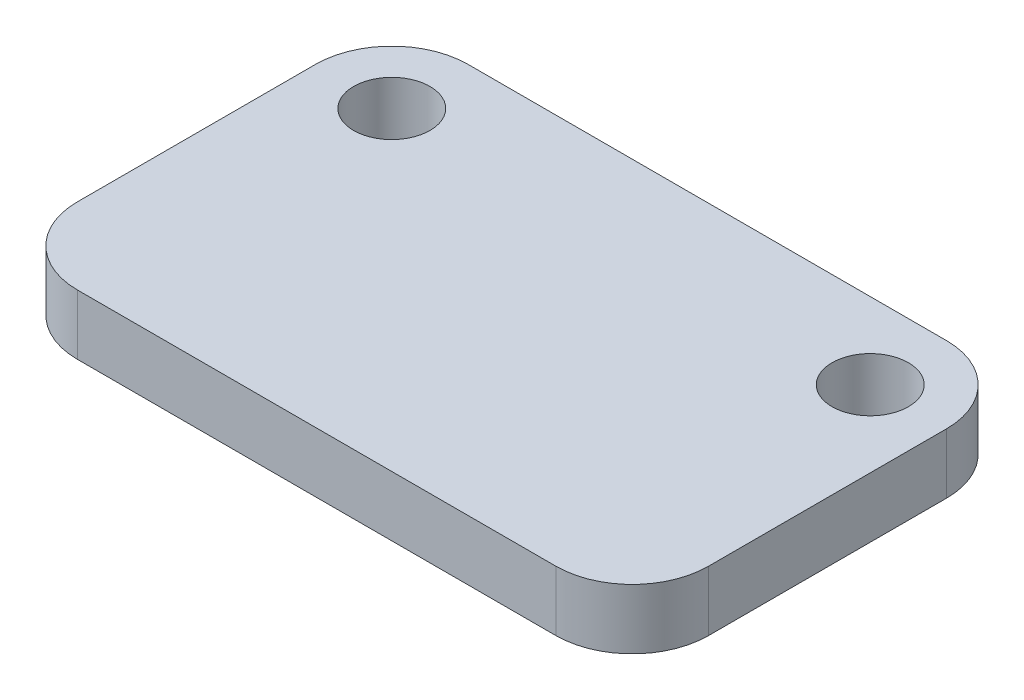
SolidWorks part; units mm, degrees
ref_plane "Front Plane" through (0, 0, 0) normal (0, 0, 1) x (1, 0, 0)
ref_plane "Top Plane" through (0, 0, 0) normal (0, 1, 0) x (1, 0, 0)
ref_plane "Right Plane" through (0, 0, 0) normal (1, 0, 0) x (0, 0, -1)
sketch "Sketch1" plane through (0, 0, 0) normal (0, 1, 0) x (1, 0, 0)
  line L1 (0, 0) -> (21, 0)
  line L2 (0, 0) -> (0, 13)
  line L3 (0, 13) -> (21, 13)
  line L4 (21, 0) -> (21, 13)
  dimension "D1" = 21
  dimension "D2" = 13
extrude "Boss-Extrude1" add sketch "Sketch1" along normal blind 2
sketch "Sketch2" plane through (0, 2, 0) normal (0, 1, 0) x (1, 0, 0)
  line L0 (21, 13) -> (0, 13) construction
  line L1 (0, 13) -> (0, 0) construction
  line L2 (10.5, 13) -> (10.5, 0) construction
  line L3 (0, 0) -> (21, 0) construction
  circle A0 centre (2.54, 10.46) radius 1.27
  circle A1 centre (18.46, 10.46) radius 1.27
  point P4 (0, 0)
  dimension "D1" = 2.54
  dimension "D2" = 2.54
  dimension "D3" = 2.54
extrude "Cut-Extrude1" cut sketch "Sketch2" against normal through all
fillet "Fillet1" radius 2.54 4 edges at (21, 1, -13) (21, 1, 0) (0, 1, 0) (0, 1, -13)
